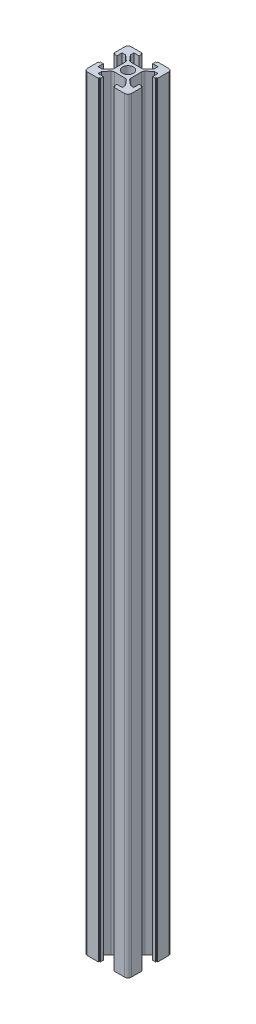
SolidWorks part; units mm, degrees
ref_plane "Front Plane" through (0, 0, 0) normal (0, 0, 1) x (1, 0, 0)
ref_plane "Top Plane" through (0, 0, 0) normal (0, 1, 0) x (1, 0, 0)
ref_plane "Right Plane" through (0, 0, 0) normal (1, 0, 0) x (0, 0, -1)
sketch "Sketch1" plane through (0, 0, 0) normal (0, 1, 0) x (1, 0, 0)
  line L0 (10, 0) -> (3.8, 0) construction
  line L1 (-8.5, -10) -> (8.5, -10)
  line L2 (-10, -8.5) -> (-10, 8.5)
  line L3 (-8.5, 10) -> (8.5, 10)
  line L4 (10, -8.5) -> (10, -3.6)
  line L5 (-10, -10) -> (10, 10) construction
  line L6 (-10, 10) -> (10, -10) construction
  line L7 (3.8, -2.4101) -> (3.8, 2.4101)
  line L8 (9.5, -3.1) -> (9.5, 3.1)
  line L9 (9.5, 3.1) -> (8.2, 3.1)
  line L10 (9.5, 3.1) -> (9.5, 3.6)
  line L11 (9.5, -3.1) -> (9.5, -3.6)
  line L12 (9.5, -3.6) -> (10, -3.6)
  line L13 (9.5, 3.6) -> (10, 3.6)
  line L14 (10, 3.6) -> (10, 8.5)
  line L15 (9.5, -3.1) -> (8.2, -3.1)
  line L16 (8.2, -3.1) -> (3.8, -3.1) construction
  line L17 (8.2, 3.1) -> (3.8, 3.1) construction
  line L18 (8.2, 3.1) -> (8.2, 5.5)
  line L19 (8.2, -3.1) -> (8.2, -5.5)
  line L20 (8.2, -5.5) -> (6.6, -5.5)
  line L21 (8.2, 5.5) -> (6.6, 5.5)
  line L22 (6.6, 5.5) -> (4.3238, 3.549)
  line L23 (6.6, -5.5) -> (4.3238, -3.549)
  line L24 (-5.5, -6.6) -> (-3.549, -4.3238)
  line L25 (-5.5, -8.2) -> (-5.5, -6.6)
  line L26 (-3.1, -8.2) -> (-5.5, -8.2)
  line L27 (-2.4101, -3.8) -> (2.4101, -3.8)
  line L28 (5.5, -6.6) -> (3.549, -4.3238)
  line L29 (5.5, -8.2) -> (5.5, -6.6)
  line L30 (3.1, -8.2) -> (5.5, -8.2)
  line L31 (3.1, -9.5) -> (3.1, -8.2)
  line L32 (3.1, -9.5) -> (3.6, -9.5)
  line L33 (3.6, -9.5) -> (3.6, -10)
  line L34 (-3.6, -9.5) -> (-3.6, -10)
  line L35 (-3.1, -9.5) -> (-3.6, -9.5)
  line L36 (-3.1, -9.5) -> (-3.1, -8.2)
  line L37 (-6.6, 5.5) -> (-4.3238, 3.549)
  line L38 (-8.2, 5.5) -> (-6.6, 5.5)
  line L39 (-8.2, 3.1) -> (-8.2, 5.5)
  line L40 (-3.8, 2.4101) -> (-3.8, -2.4101)
  line L41 (-6.6, -5.5) -> (-4.3238, -3.549)
  line L42 (-8.2, -5.5) -> (-6.6, -5.5)
  line L43 (-8.2, -3.1) -> (-8.2, -5.5)
  line L44 (-9.5, -3.1) -> (-8.2, -3.1)
  line L45 (-9.5, -3.1) -> (-9.5, -3.6)
  line L46 (-9.5, -3.6) -> (-10, -3.6)
  line L47 (-9.5, 3.6) -> (-10, 3.6)
  line L48 (-9.5, 3.1) -> (-9.5, 3.6)
  line L49 (-9.5, 3.1) -> (-8.2, 3.1)
  line L50 (5.5, 6.6) -> (3.549, 4.3238)
  line L51 (5.5, 8.2) -> (5.5, 6.6)
  line L52 (3.1, 8.2) -> (5.5, 8.2)
  line L53 (2.4101, 3.8) -> (-2.4101, 3.8)
  line L54 (-5.5, 6.6) -> (-3.549, 4.3238)
  line L55 (-5.5, 8.2) -> (-5.5, 6.6)
  line L56 (-3.1, 8.2) -> (-5.5, 8.2)
  line L57 (-3.1, 9.5) -> (-3.1, 8.2)
  line L58 (-3.1, 9.5) -> (-3.6, 9.5)
  line L59 (-3.6, 9.5) -> (-3.6, 10)
  line L60 (3.6, 9.5) -> (3.6, 10)
  line L61 (3.1, 9.5) -> (3.6, 9.5)
  line L62 (3.1, 9.5) -> (3.1, 8.2)
  circle A0 centre (0, 0) radius 2.5
  arc A1 (8.5, 10) -> (10, 8.5) centre (8.5, 8.5) cw
  arc A2 (8.5, -10) -> (10, -8.5) centre (8.5, -8.5) ccw
  arc A3 (-8.5, -10) -> (-10, -8.5) centre (-8.5, -8.5) cw
  arc A4 (-10, 8.5) -> (-8.5, 10) centre (-8.5, 8.5) cw
  arc A5 (3.8, -2.4101) -> (4.3238, -3.549) centre (5.3, -2.4101) ccw
  arc A6 (4.3238, 3.549) -> (3.8, 2.4101) centre (5.3, 2.4101) ccw
  arc A7 (-2.4101, -3.8) -> (-3.549, -4.3238) centre (-2.4101, -5.3) ccw
  arc A8 (3.549, -4.3238) -> (2.4101, -3.8) centre (2.4101, -5.3) ccw
  arc A9 (-3.8, 2.4101) -> (-4.3238, 3.549) centre (-5.3, 2.4101) ccw
  arc A10 (-4.3238, -3.549) -> (-3.8, -2.4101) centre (-5.3, -2.4101) ccw
  arc A11 (2.4101, 3.8) -> (3.549, 4.3238) centre (2.4101, 5.3) ccw
  arc A12 (-3.549, 4.3238) -> (-2.4101, 3.8) centre (-2.4101, 5.3) ccw
  point P0 (0, 0)
  point P25 (3.8, 0)
  point P28 (8.5, 0)
  dimension "D3" = 5
  dimension "D4" = 1.5
  dimension "D5" = 1.5
  dimension "D1" = 20
  dimension "D2" = 20
  dimension "D6" = 6.2
  dimension "D7" = 6.2
  dimension "D8" = 0.5
  dimension "D9" = 1.3
  dimension "D10" = 4
extrude "Boss-Extrude1" add sketch "Sketch1" along normal blind 350 contours A12 L54 L55 L56 L57 L58 L59 L3 A4 L2 L47 L48 L49 L39 L38 L37 A9 L40 A10 L41 L42 L43 L44 L45 L46 A3 L1 L34 L35 L36 L26 L25 L24 A7 L27 A8 L28 L29 L30 L31 L32 L33 A2 L4 L12 L11 L15 L19 L20
